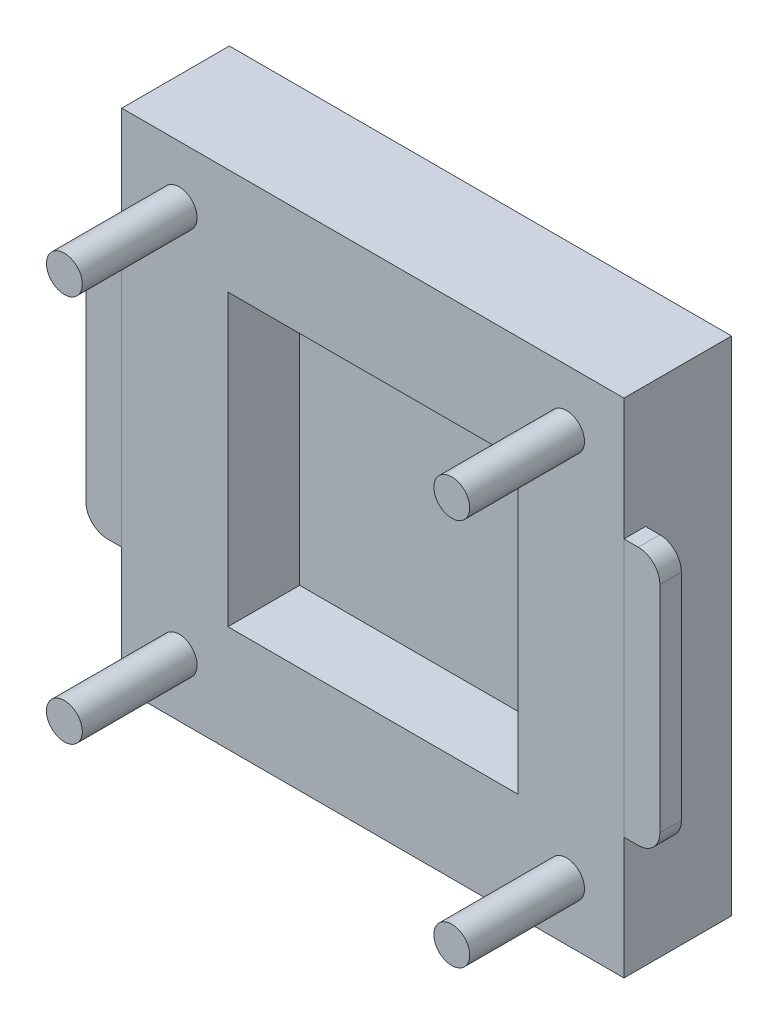
SolidWorks part; units mm, degrees
ref_plane "前视基准面" through (0, 0, 0) normal (0, 0, 1) x (1, 0, 0)
ref_plane "上视基准面" through (0, 0, 0) normal (0, 1, 0) x (1, 0, 0)
ref_plane "右视基准面" through (0, 0, 0) normal (1, 0, 0) x (0, 0, -1)
sketch "草图1" plane through (0, 0, 0) normal (0, 0, 1) x (1, 0, 0)
  line L1 (0, 0) -> (70, 0)
  line L2 (0, 0) -> (0, 70)
  line L3 (0, 70) -> (70, 70)
  line L4 (70, 0) -> (70, 70)
  dimension "D1" = 70
  dimension "D2" = 70
extrude "凸台-拉伸1" add sketch "草图1" along normal blind 15
sketch "草图2" plane through (0, 0, 15) normal (0, 0, 1) x (1, 0, 0)
  line L0 (0, 70) -> (0, 0) construction
  line L1 (14.8, 55.2) -> (55.2, 55.2)
  line L2 (14.8, 55.2) -> (14.8, 14.8)
  line L3 (14.8, 14.8) -> (55.2, 14.8)
  line L4 (55.2, 55.2) -> (55.2, 14.8)
  line L5 (0, 0) -> (70, 0) construction
  line L6 (70, 70) -> (0, 70) construction
  dimension "D1" = 14.8
  dimension "D2" = 14.8
  dimension "D3" = 40.4
extrude "切除-拉伸1" cut sketch "草图2" against normal blind 10
sketch "草图3" plane through (0, 0, 15) normal (0, 0, 1) x (1, 0, 0)
  line L0 (35, 70) -> (35, 0) construction
  line L3 (0, 35) -> (70, 35) construction
  line L6 (0, 70) -> (0, 0) construction
  line L7 (70, 70) -> (0, 70) construction
  circle A0 centre (8, 62) radius 2.5
  circle A1 centre (62, 62) radius 2.5
  circle A2 centre (62, 8) radius 2.5
  circle A3 centre (8, 8) radius 2.5
  point P16 (35, 35)
  point P18 (0, 35)
  point P19 (35, 70)
  dimension "D1" = 5
  dimension "D2" = 8
  dimension "D3" = 8
extrude "凸台-拉伸2" add sketch "草图3" along normal blind 16
sketch "草图5" plane through (0, 0, 15) normal (0, 0, 1) x (1, 0, 0)
  line L0 (35, 70) -> (35, 0) construction
  line L4 (0, 35) -> (70, 35) construction
  line L6 (0, 70) -> (0, 0) construction
  line L7 (70, 70) -> (0, 70) construction
  line L9 (-2, 53) -> (0, 53)
  line L10 (-5, 50) -> (-5, 20)
  line L11 (-2, 17) -> (0, 17)
  line L12 (0, 53) -> (0, 17)
  line L16 (72, 17) -> (70, 17)
  line L17 (70, 53) -> (70, 17)
  line L18 (72, 53) -> (70, 53)
  line L19 (75, 50) -> (75, 20)
  arc A0 (-5, 20) -> (-2, 17) centre (-2, 20) ccw
  arc A1 (-2, 53) -> (-5, 50) centre (-2, 50) ccw
  arc A2 (75, 20) -> (72, 17) centre (72, 20) cw
  arc A3 (72, 53) -> (75, 50) centre (72, 50) cw
  point P3 (35, 70)
  point P9 (0, 35)
  point P14 (-5, 35)
  point P17 (-5, 17)
  point P20 (-5, 53)
  dimension "D3" = 3
  dimension "D1" = 5
  dimension "D2" = 36
extrude "凸台-拉伸3" add sketch "草图5" against normal blind 3 separate body
